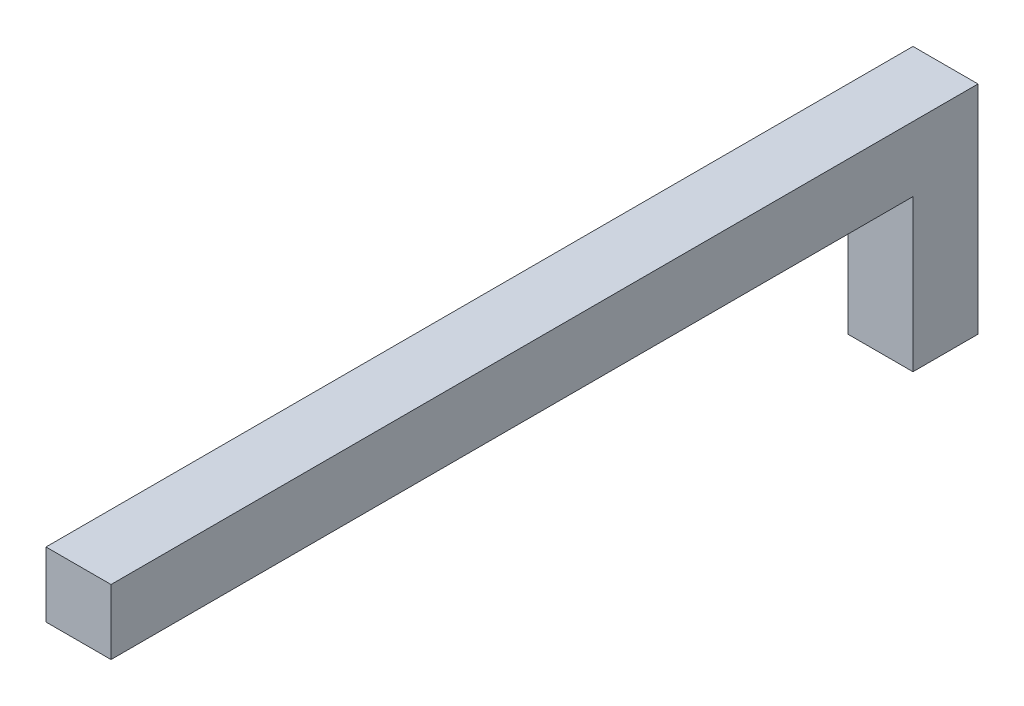
SolidWorks part; units mm, degrees
material "1060 Alloy"
ref_plane "Front Plane" through (0, 0, 0) normal (0, 0, 1) x (1, 0, 0)
ref_plane "Top Plane" through (0, 0, 0) normal (0, 1, 0) x (1, 0, 0)
ref_plane "Right Plane" through (0, 0, 0) normal (1, 0, 0) x (0, 0, -1)
sketch "Sketch1" plane through (0, 0, 0) normal (1, 0, 0) x (0, 0, -1)
  line L0 (-0.3, 0) -> (0.3, 0)
  line L1 (0.3, 0) -> (0.3, 2)
  line L2 (0.3, 2) -> (-7.7, 2)
  line L3 (-7.7, 2) -> (-7.7, 1.4)
  line L4 (-7.7, 1.4) -> (-0.3, 1.4)
  line L5 (-0.3, 1.4) -> (-0.3, 0)
  point P4 (0, 0)
  dimension "D1" = 0.6
  dimension "D2" = 8
  dimension "D3" = 2
extrude "Boss-Extrude1" add sketch "Sketch1" along normal mid plane 0.6
